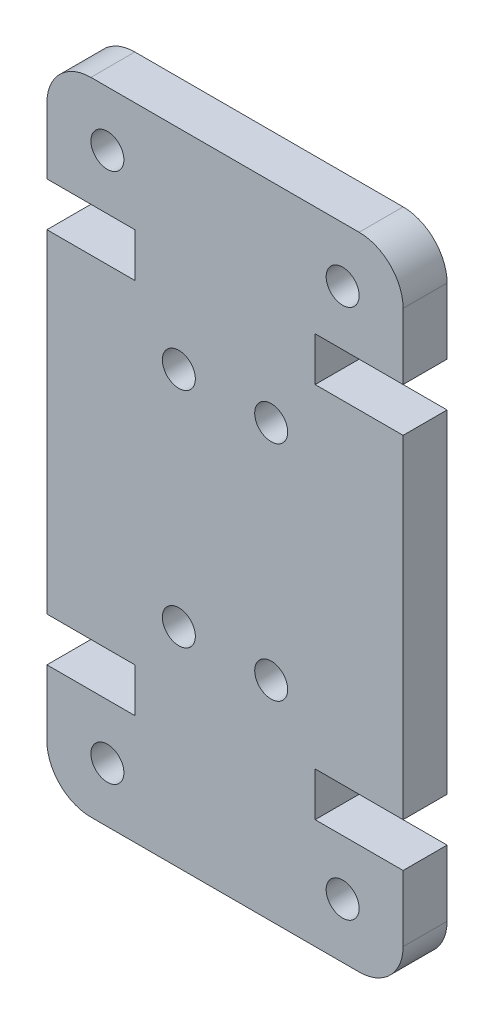
SolidWorks part; units mm, degrees
ref_plane "Front Plane" through (0, 0, 0) normal (0, 0, 1) x (1, 0, 0)
ref_plane "Top Plane" through (0, 0, 0) normal (0, 1, 0) x (1, 0, 0)
ref_plane "Right Plane" through (0, 0, 0) normal (1, 0, 0) x (0, 0, -1)
sketch "Sketch1" plane through (0, 0, 0) normal (0, 0, 1) x (1, 0, 0)
  line L0 (0, 22.14) -> (0, 7)
  line L1 (16.2, 2) -> (16.2, 5)
  line L2 (12.2, 5) -> (16.2, 5)
  line L3 (2, 0) -> (14.2, 0)
  line L4 (16.2, 7) -> (12.2, 7)
  line L5 (12.2, 7) -> (12.2, 5)
  line L6 (16.2, 22.14) -> (16.2, 7)
  line L7 (4, 7) -> (4, 5)
  line L8 (0, 27.14) -> (0, 24.14)
  line L9 (4, 24.14) -> (0, 24.14)
  line L10 (0, 7) -> (4, 7)
  line L11 (0, 22.14) -> (4, 22.14)
  line L12 (4, 5) -> (0, 5)
  line L13 (4, 22.14) -> (4, 24.14)
  line L14 (12.2, 22.14) -> (12.2, 24.14)
  line L15 (16.2, 22.14) -> (12.2, 22.14)
  line L16 (0, 2) -> (0, 5)
  line L17 (2, 29.14) -> (14.2, 29.14)
  line L18 (12.2, 24.14) -> (16.2, 24.14)
  line L19 (16.2, 27.14) -> (16.2, 24.14)
  line L20 (8.1, 29.14) -> (8.1, 0) construction
  line L21 (0, 14.57) -> (16.2, 14.57) construction
  circle A0 centre (13.45, 2.5) radius 0.75
  circle A1 centre (10.2, 9.5) radius 0.75
  arc A2 (16.2, 2) -> (14.2, 0) centre (14.2, 2) cw
  circle A3 centre (2.75, 26.64) radius 0.75
  circle A4 centre (6, 19.64) radius 0.75
  arc A5 (0, 2) -> (2, 0) centre (2, 2) ccw
  arc A6 (0, 27.14) -> (2, 29.14) centre (2, 27.14) cw
  circle A7 centre (6, 9.5) radius 0.75
  arc A8 (16.2, 27.14) -> (14.2, 29.14) centre (14.2, 27.14) ccw
  circle A9 centre (2.75, 2.5) radius 0.75
  circle A10 centre (10.2, 19.64) radius 0.75
  circle A11 centre (13.45, 26.64) radius 0.75
  point P15 (8.1, 14.57)
  dimension "D1" = 1.5
  dimension "D2" = 2
  dimension "D3" = 2.75
  dimension "D4" = 6
  dimension "D5" = 8.1
  dimension "D6" = 2.5
  dimension "D7" = 5
  dimension "D9" = 9.5
  dimension "D10" = 14.57
extrude "Boss-Extrude1" add sketch "Sketch1" along normal blind 2
equation "\"D5@Sketch1\"= \"fingerWidth@parametersSketch@prostheticParameters.SLDPRT\" / 2'PIP width"
equation "\"D10@Sketch1\"= ( \"HL@parametersSketch@prostheticParameters.SLDPRT\" * 0.244 - 4 - 12 ) / 2 'PIP length - Sil.Sht PIP - Sil. Sht MIP"
